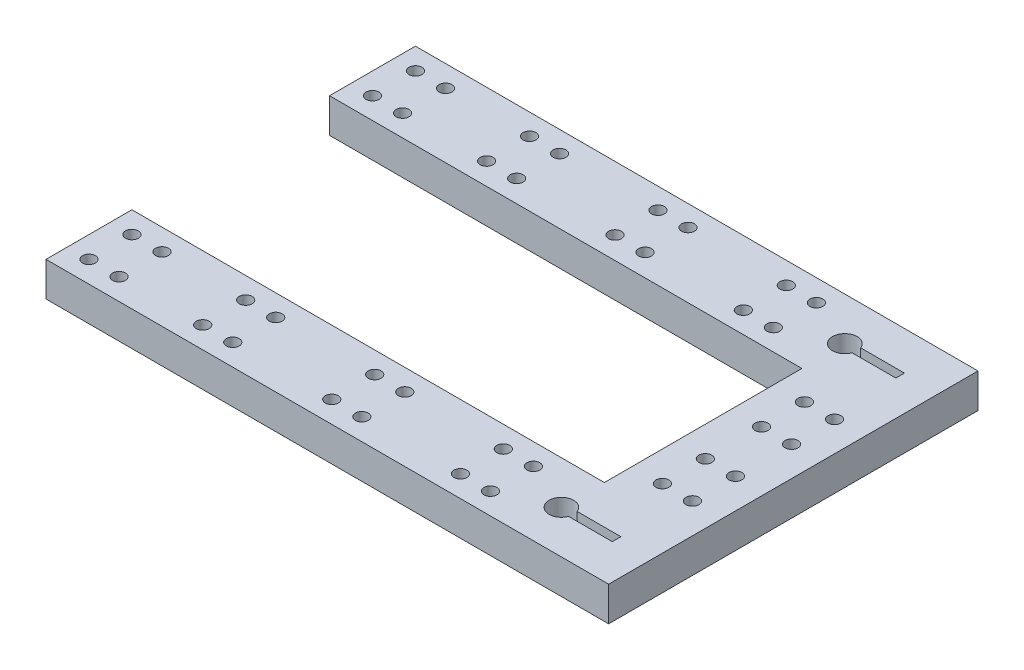
SolidWorks part; units mm, degrees
ref_plane "Front Plane" through (0, 0, 0) normal (0, 0, 1) x (1, 0, 0)
ref_plane "Top Plane" through (0, 0, 0) normal (0, 1, 0) x (1, 0, 0)
ref_plane "Right Plane" through (0, 0, 0) normal (1, 0, 0) x (0, 0, -1)
sketch "Sketch1" plane through (0, 0, 0) normal (0, 1, 0) x (1, 0, 0)
  line L0 (130.9822, 32.9968) -> (21, 32.9968)
  line L6 (130.9822, 32.9968) -> (130.9822, 40.4968)
  line L7 (21, 32.9968) -> (21, 42.9968)
  line L8 (21, 42.9968) -> (144.4822, 42.9968)
  line L9 (130.9822, 32.9968) -> (130.9822, -33.0032)
  line L10 (133.8322, -32) -> (143.8322, -32)
  line L11 (130.9822, -33.0032) -> (20.9822, -33.0032)
  line L12 (21, 32.9968) -> (21, 22.9968)
  line L13 (21, 22.9968) -> (144.4822, 22.9968)
  line L14 (20.9822, -33.0032) -> (20.9822, -23.0032)
  line L15 (20.9822, -23.0032) -> (144.4822, -23.0032)
  line L16 (151.9822, 32.9968) -> (151.9822, 42.9968)
  line L17 (151.9822, 42.9968) -> (144.4822, 42.9968)
  line L18 (151.9822, 42.9968) -> (151.9822, -43.0032)
  line L19 (151.9822, -43.0032) -> (144.4822, -43.0032)
  line L20 (143.8322, -32) -> (143.8322, -34)
  line L21 (20.9822, -33.0032) -> (20.9822, -43.0032)
  line L22 (20.9822, -43.0032) -> (144.4822, -43.0032)
  line L23 (143.8322, -34) -> (133.8322, -34)
  line L24 (26, 32.9968) -> (56, 32.9968)
  line L25 (133.85, 33.9968) -> (133.67, 33.9968)
  line L26 (56, 32.9968) -> (86, 32.9968)
  line L27 (133.85, 31.9968) -> (133.67, 31.9968)
  line L28 (130.9822, -33.0032) -> (133.8322, -33.0032)
  line L29 (133.85, 33.9968) -> (143.85, 33.9968)
  line L30 (143.85, 33.9968) -> (143.85, 31.9968)
  line L31 (133.8322, -34) -> (133.6522, -34)
  line L32 (133.8322, -32) -> (133.6522, -32)
  line L33 (21, 32.9968) -> (26, 32.9968)
  line L34 (143.85, 31.9968) -> (133.85, 31.9968)
  line L35 (86, 32.9968) -> (116, 32.9968)
  line L36 (25.9822, -33.0032) -> (55.9822, -33.0032)
  line L37 (20.9822, -33.0032) -> (25.9822, -33.0032)
  line L38 (55.9822, -33.0032) -> (85.9822, -33.0032)
  line L39 (85.9822, -33.0032) -> (115.9822, -33.0032)
  line L40 (130.9822, 22.9968) -> (141.4822, 22.9968)
  line L41 (141.4822, 22.9968) -> (141.4822, 11.4968)
  line L42 (141.4822, -23.0032) -> (141.4822, -11.5032)
  line L43 (133.8322, -34) -> (133.2168, -34)
  line L44 (133.8322, -32) -> (133.1367, -32)
  circle A6 centre (130.9822, 32.9968) radius 2.8678
  circle A7 centre (130.9822, -33.0032) radius 2.85
  circle A8 centre (26, 37.9968) radius 1.5
  circle A9 centre (26, 27.9968) radius 1.5
  circle A10 centre (33, 27.9968) radius 1.5
  circle A11 centre (33, 37.9968) radius 1.5
  circle A12 centre (25.9822, -28.0032) radius 1.5
  circle A13 centre (25.9822, -38.0032) radius 1.5
  circle A14 centre (32.9822, -38.0032) radius 1.5
  circle A15 centre (32.9822, -28.0032) radius 1.5
  circle A16 centre (52.452, 38.1086) radius 1.5
  circle A17 centre (52.452, 28.1086) radius 1.5
  circle A18 centre (59.452, 28.1086) radius 1.5
  circle A19 centre (59.452, 38.1086) radius 1.5
  circle A20 centre (82.3101, 38.1532) radius 1.5
  circle A21 centre (82.3101, 28.1532) radius 1.5
  circle A22 centre (89.3101, 28.1532) radius 1.5
  circle A23 centre (89.3101, 38.1532) radius 1.5
  circle A24 centre (112.41, 37.9311) radius 1.5
  circle A25 centre (112.41, 27.9311) radius 1.5
  circle A26 centre (119.41, 27.9311) radius 1.5
  circle A27 centre (119.41, 37.9311) radius 1.5
  circle A28 centre (52.4471, -27.9782) radius 1.5
  circle A29 centre (52.4471, -37.9782) radius 1.5
  circle A30 centre (59.4471, -37.9782) radius 1.5
  circle A31 centre (59.4471, -27.9782) radius 1.5
  circle A32 centre (82.4833, -27.9712) radius 1.5
  circle A33 centre (82.4833, -37.9712) radius 1.5
  circle A34 centre (89.4833, -37.9712) radius 1.5
  circle A35 centre (89.4833, -27.9712) radius 1.5
  circle A36 centre (112.4668, -28.0056) radius 1.5
  circle A37 centre (112.4668, -38.0056) radius 1.5
  circle A38 centre (119.4668, -38.0056) radius 1.5
  circle A39 centre (119.4668, -28.0056) radius 1.5
  circle A40 centre (138.0447, 16.5309) radius 1.5
  circle A41 centre (138.0447, 6.5309) radius 1.5
  circle A42 centre (145.0447, 6.5309) radius 1.5
  circle A43 centre (145.0447, 16.5309) radius 1.5
  circle A44 centre (137.962, -6.4687) radius 1.5
  circle A45 centre (137.962, -16.4687) radius 1.5
  circle A46 centre (144.962, -16.4687) radius 1.5
  circle A47 centre (144.962, -6.4687) radius 1.5
extrude "Boss-Extrude1" add sketch "Sketch1" along normal blind 8
